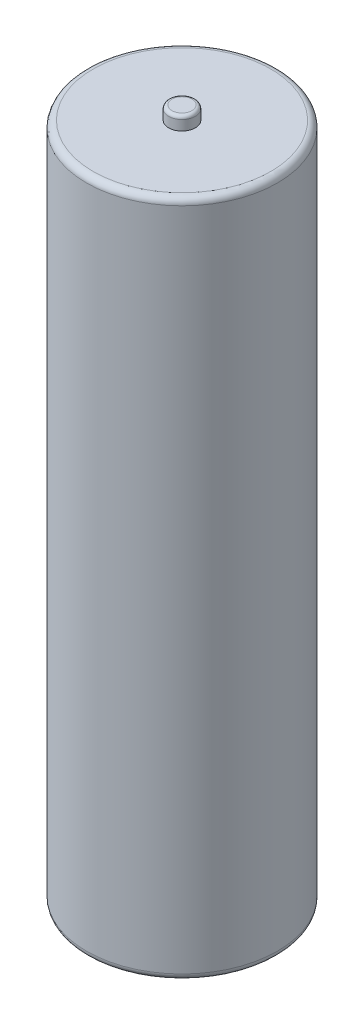
SolidWorks part; units mm, degrees
material "6063-T6"
ref_plane "Front Plane" through (0, 0, 0) normal (0, 0, 1) x (1, 0, 0)
ref_plane "Top Plane" through (0, 0, 0) normal (0, 1, 0) x (1, 0, 0)
ref_plane "Right Plane" through (0, 0, 0) normal (1, 0, 0) x (0, 0, -1)
sketch "Sketch1" plane through (0, 0, 0) normal (0, 1, 0) x (1, 0, 0)
  circle A0 centre (0, 0) radius 7.175
  dimension "D1" = 14.35
extrude "Boss-Extrude1" add sketch "Sketch1" along normal blind 51
fillet "Fillet1" radius 0.5 2 edges at (0, 51, 7.175) (0, 0, 7.175)
sketch "Sketch2" plane through (0, 51, 0) normal (0, 1, 0) x (1, 0, 0)
  circle A0 centre (0, 0) radius 1
extrude "Boss-Extrude2" add sketch "Sketch2" along normal blind 1
fillet "Fillet2" radius 0.25 1 edges at (0, 52, 1)
